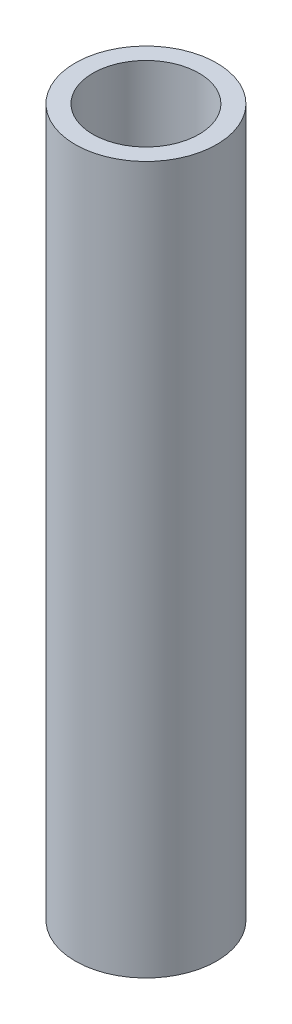
SolidWorks part; units mm, degrees
ref_plane "Front Plane" through (0, 0, 0) normal (0, 0, 1) x (1, 0, 0)
ref_plane "Top Plane" through (0, 0, 0) normal (0, 1, 0) x (1, 0, 0)
ref_plane "Right Plane" through (0, 0, 0) normal (1, 0, 0) x (0, 0, -1)
sketch "Sketch1" plane through (0, 0, 0) normal (0, 1, 0) x (1, 0, 0)
  circle A0 centre (0, 0) radius 10
  circle A1 centre (0, 0) radius 7.5
  dimension "D1" = 20
  dimension "D2" = 15
extrude "Boss-Extrude1" add sketch "Sketch1" along normal blind 100
